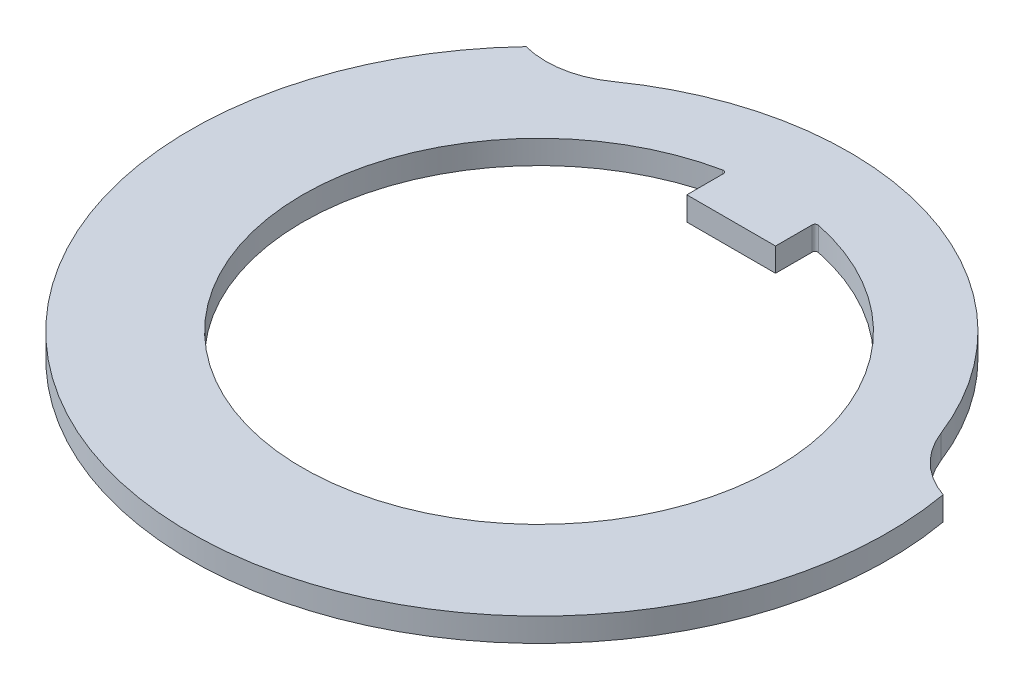
SolidWorks part; units mm, degrees
ref_plane "Front Plane" through (0, 0, 0) normal (0, 0, 1) x (1, 0, 0)
ref_plane "Top Plane" through (0, 0, 0) normal (0, 1, 0) x (1, 0, 0)
ref_plane "Right Plane" through (0, 0, 0) normal (1, 0, 0) x (0, 0, -1)
sketch "Sketch1" plane through (0, 0, 0) normal (0, 1, 0) x (1, 0, 0)
  line L0 (0, 11.8) -> (0, -10.5) construction
  line L1 (0, 0) -> (-8.5594, 8.1226) construction
  line L2 (0, 0) -> (11.6207, 2.049) construction
  line L5 (0, 0) -> (11.8, 0) construction
  line L6 (-1.5, 6.5) -> (1.5, 6.5)
  line L7 (-1.5, 6.5) -> (-1.5, 7.8581)
  line L9 (1.5, 6.5) -> (1.5, 7.8581)
  line L10 (-1.5, 6.5) -> (0, 8) construction
  line L11 (0, 8) -> (1.5, 6.5) construction
  arc A1 (-1.5, 7.8581) -> (1.5, 7.8581) centre (0, 0) ccw
  arc A5 (9.7868, 3.8037) -> (-6.0617, 8.5736) centre (0, 0) ccw
  arc A6 (-6.0617, 8.5736) -> (-8.5594, 8.1226) centre (-7.7936, 11.0232) cw
  arc A7 (11.6207, 2.049) -> (9.7868, 3.8037) centre (12.583, 4.8905) cw
  arc A8 (-8.5594, 8.1226) -> (11.6207, 2.049) centre (0, 0) ccw
  point P4 (0, 8)
  point P25 (0, 0)
  dimension "D2" = 16
  dimension "D3" = 11.8
  dimension "D6" = 126.5
  dimension "D7" = 3
  dimension "D5" = 10.5
  dimension "D8" = 3
  dimension "D4" = 46.5
  dimension "D10" = 6.5
  dimension "D11" = 3
extrude "Boss-Extrude1" add sketch "Sketch1" along normal blind 0.8
fillet "Fillet1" radius 0.1 2 edges at (-1.5, 0.4, -7.8581) (1.5, 0.4, -7.8581)
